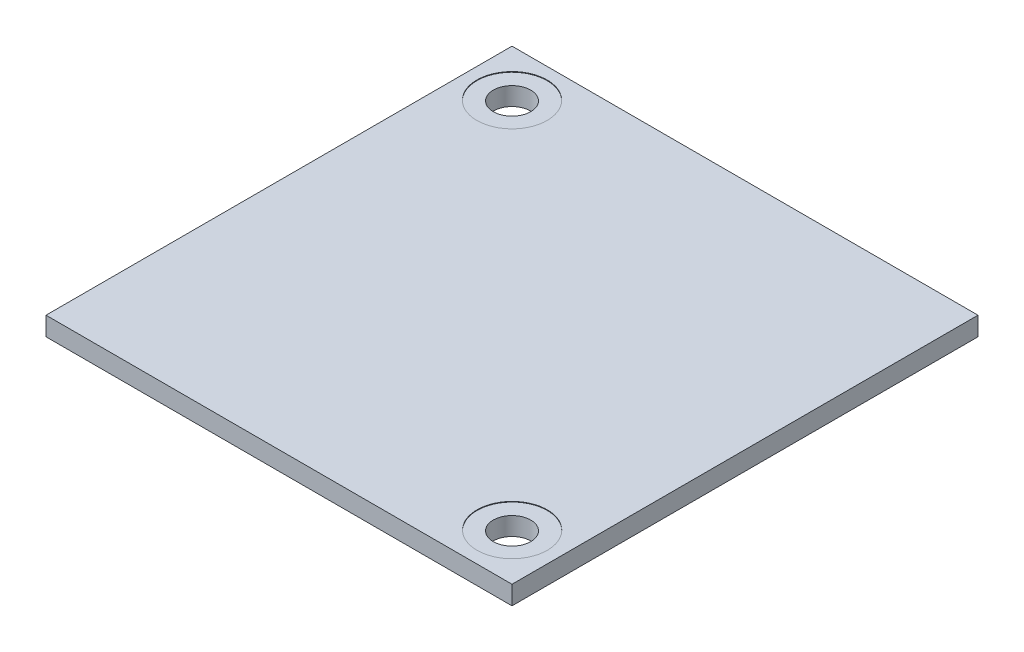
SolidWorks part; units mm, degrees
ref_plane "Front Plane" through (0, 0, 0) normal (0, 0, 1) x (1, 0, 0)
ref_plane "Top Plane" through (0, 0, 0) normal (0, 1, 0) x (1, 0, 0)
ref_plane "Right Plane" through (0, 0, 0) normal (1, 0, 0) x (0, 0, -1)
sketch "Sketch1" plane through (0, 0, 0) normal (0, 1, 0) x (1, 0, 0)
  line L1 (-20.2, 20.2) -> (19.6, 20.2)
  line L3 (-20.2, 20.2) -> (-20.2, -19.6)
  line L4 (-20.2, -19.6) -> (19.6, -19.6)
  line L5 (19.6, 20.2) -> (19.6, -19.6)
  point P0 (0, 0)
  dimension "D1" = 39.8
  dimension "D2" = 39.8
extrude "Boss-Extrude1" add sketch "Sketch1" along normal blind 1.6
sketch "Sketch10" plane through (0, 1.6, 0) normal (0, 1, 0) x (1, 0, 0)
  line L0 (-0.3, 20.2) -> (-0.3, -19.6) construction
  line L1 (19.6, 20.2) -> (-20.2, 20.2) construction
  line L2 (-20.2, -19.6) -> (19.6, -19.6) construction
  line L3 (-20.2, 0.3) -> (19.6, 0.3) construction
  line L4 (-20.2, 20.2) -> (-20.2, -19.6) construction
  line L5 (19.6, -19.6) -> (19.6, 20.2) construction
  line L6 (-16.2, 20.2) -> (-16.2, 16.2) construction
  line L7 (-16.2, 16.2) -> (-20.2, 16.2) construction
  circle A0 centre (-16.2, 16.2) radius 3
  circle A1 centre (15.6, -15.5867) radius 3
  point P20 (-0.3033, 0.3034)
  dimension "D3" = 2
  dimension "D1" = 4
  dimension "D2" = 4
extrude "Cut-Extrude6" cut sketch "Sketch10" against normal blind 0.05
sketch "Sketch11" plane through (0, 1.6, 0) normal (0, 1, 0) x (1, 0, 0)
  line L0 (-0.3, 20.2) -> (-0.3, -19.6) construction
  line L1 (19.6, 20.2) -> (-20.2, 20.2) construction
  line L2 (-20.2, -19.6) -> (19.6, -19.6) construction
  line L3 (-20.2, 0.3) -> (19.6, 0.3) construction
  line L4 (-20.2, 20.2) -> (-20.2, -19.6) construction
  line L5 (19.6, -19.6) -> (19.6, 20.2) construction
  circle A0 centre (-16.2, 16.2) radius 1.6
  circle A1 centre (15.6, -15.6) radius 1.6
  point P19 (-0.2999, 0.3001)
  dimension "D1" = 2
extrude "Cut-Extrude7" cut sketch "Sketch11" against normal blind 1.6
